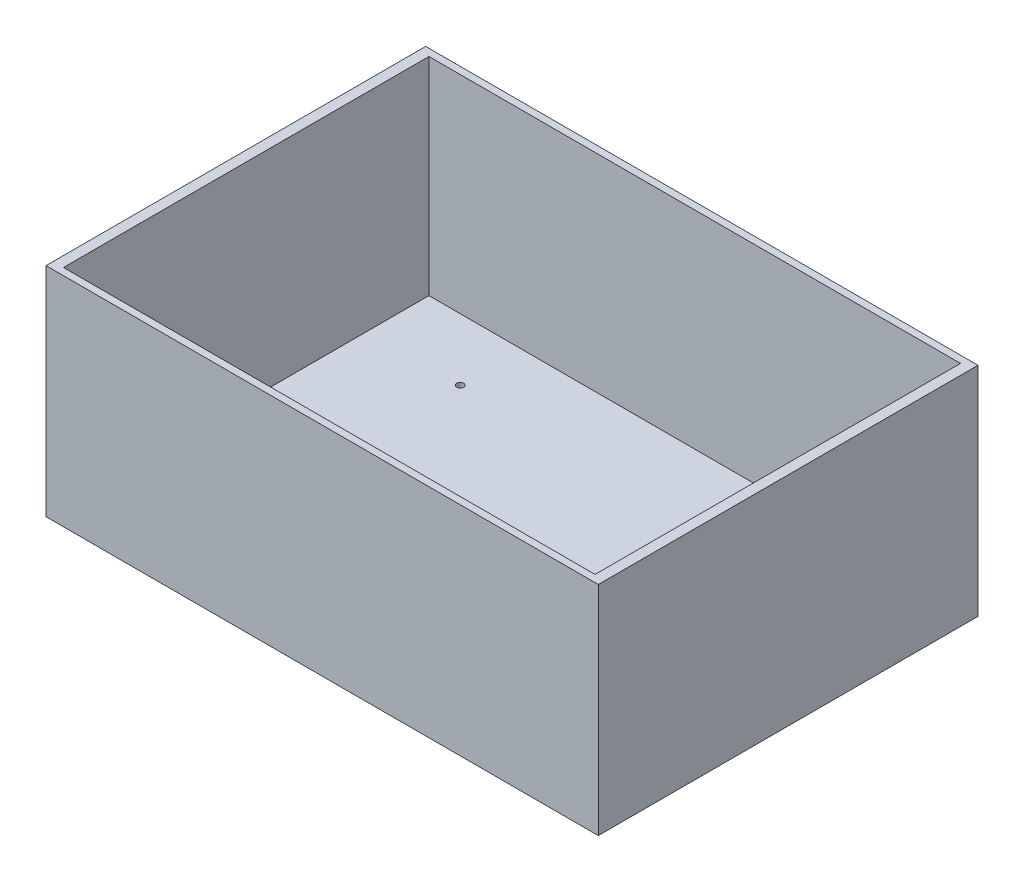
SolidWorks part; units mm, degrees
ref_plane "前视基准面" through (0, 0, 0) normal (0, 0, 1) x (1, 0, 0)
ref_plane "上视基准面" through (0, 0, 0) normal (0, 1, 0) x (1, 0, 0)
ref_plane "右视基准面" through (0, 0, 0) normal (1, 0, 0) x (0, 0, -1)
other "Configuration Table"
sketch "草图1" plane through (0, 0, 0) normal (0, 1, 0) x (1, 0, 0)
  line L1 (-80, 55) -> (80, 55)
  line L2 (-80, 55) -> (-80, -55)
  line L3 (-80, -55) -> (80, -55)
  line L4 (80, 55) -> (80, -55)
  line L5 (-80, 55) -> (80, -55) construction
  line L6 (-80, -55) -> (80, 55) construction
  point P0 (0, 0)
  dimension "D1" = 160
  dimension "D2" = 110
extrude "凸台-拉伸1" add sketch "草图1" along normal blind 3
sketch "草图2" plane through (0, 3, 0) normal (0, 1, 0) x (1, 0, 0)
  line L1 (-80, 55) -> (80, 55)
  line L2 (-80, 55) -> (-80, -55)
  line L3 (-80, -55) -> (80, -55)
  line L4 (80, 55) -> (80, -55)
  line L5 (-80, 55) -> (80, -55) construction
  line L6 (-80, -55) -> (80, 55) construction
  line L7 (-77, 52.9375) -> (77, 52.9375)
  line L8 (-77, 52.9375) -> (-77, -52.9375)
  line L9 (-77, -52.9375) -> (77, -52.9375)
  line L10 (77, 52.9375) -> (77, -52.9375)
  line L11 (-77, 52.9375) -> (77, -52.9375) construction
  line L12 (-77, -52.9375) -> (77, 52.9375) construction
  point P0 (0, 0)
  point P7 (0, 0)
  dimension "D1" = 154
extrude "凸台-拉伸2" add sketch "草图2" along normal blind 60
sketch "草图3" plane through (0, 3, 0) normal (0, 1, 0) x (1, 0, 0)
  line L1 (-50, 35) -> (50, 35) construction
  line L2 (-50, 35) -> (-50, -35) construction
  line L3 (-50, -35) -> (50, -35) construction
  line L4 (50, 35) -> (50, -35) construction
  line L5 (-50, 35) -> (50, -35) construction
  line L6 (-50, -35) -> (50, 35) construction
  circle A0 centre (-50, 35) radius 1
  circle A1 centre (50, 35) radius 1
  circle A2 centre (50, -35) radius 1
  circle A3 centre (-50, -35) radius 1
  point P0 (0, 0)
  dimension "D3" = 2
  dimension "D4" = 2
  dimension "D5" = 2
  dimension "D6" = 2
  dimension "D1" = 100
  dimension "D2" = 70
extrude "切除-拉伸1" cut sketch "草图3" against normal blind 10
